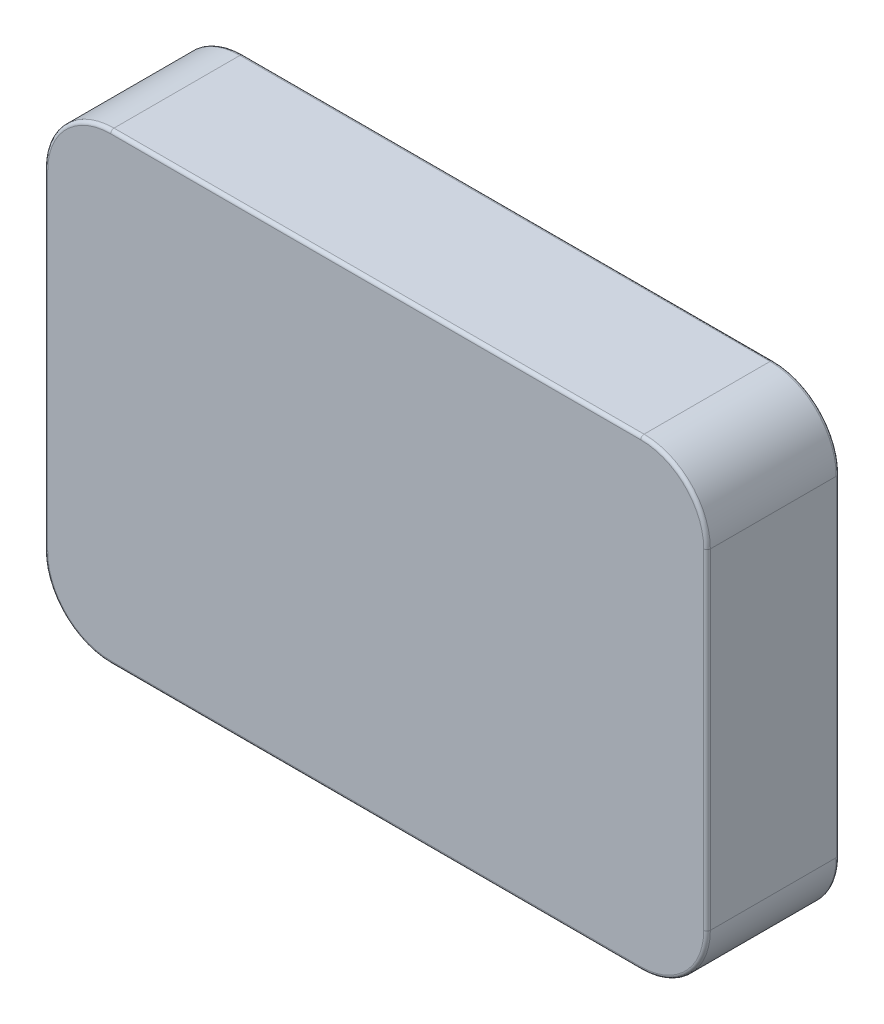
SolidWorks part; units mm, degrees
ref_plane "Front Plane" through (0, 0, 0) normal (0, 0, 1) x (1, 0, 0)
ref_plane "Top Plane" through (0, 0, 0) normal (0, 1, 0) x (1, 0, 0)
ref_plane "Right Plane" through (0, 0, 0) normal (1, 0, 0) x (0, 0, -1)
sketch "Sketch1" plane through (0, 0, 0) normal (0, 0, 1) x (1, 0, 0)
  line L1 (-50, -34.925) -> (50, -34.925)
  line L2 (-50, -34.925) -> (-50, 34.925)
  line L3 (-50, 34.925) -> (50, 34.925)
  line L4 (50, -34.925) -> (50, 34.925)
  line L5 (-50, -34.925) -> (50, 34.925) construction
  line L6 (-50, 34.925) -> (50, -34.925) construction
  point P0 (0, 0)
  dimension "D1" = 100
  dimension "D2" = 69.85
extrude "Boss-Extrude1" add sketch "Sketch1" along normal blind 20
fillet "Fillet1" radius 10 4 edges at (-50, -34.925, 10) (50, -34.925, 10) (50, 34.925, 10) (-50, 34.925, 10)
fillet "Fillet2" radius 0.5 16 edges at (47.0711, 31.9961, 0) (50, 0, 0) (47.0711, -31.9961, 0) (0, -34.925, 0) (-47.0711, -31.9961, 0) (-50, 0, 0) (-47.0711, 31.9961, 0) (47.0711, 31.9961, 20) (50, 0, 20) (47.0711, -31.9961, 20) (0, -34.925, 20) (-47.0711, -31.9961, 20) (-50, 0, 20) (-47.0711, 31.9961, 20) (0, 34.925, 0) (0, 34.925, 20)
